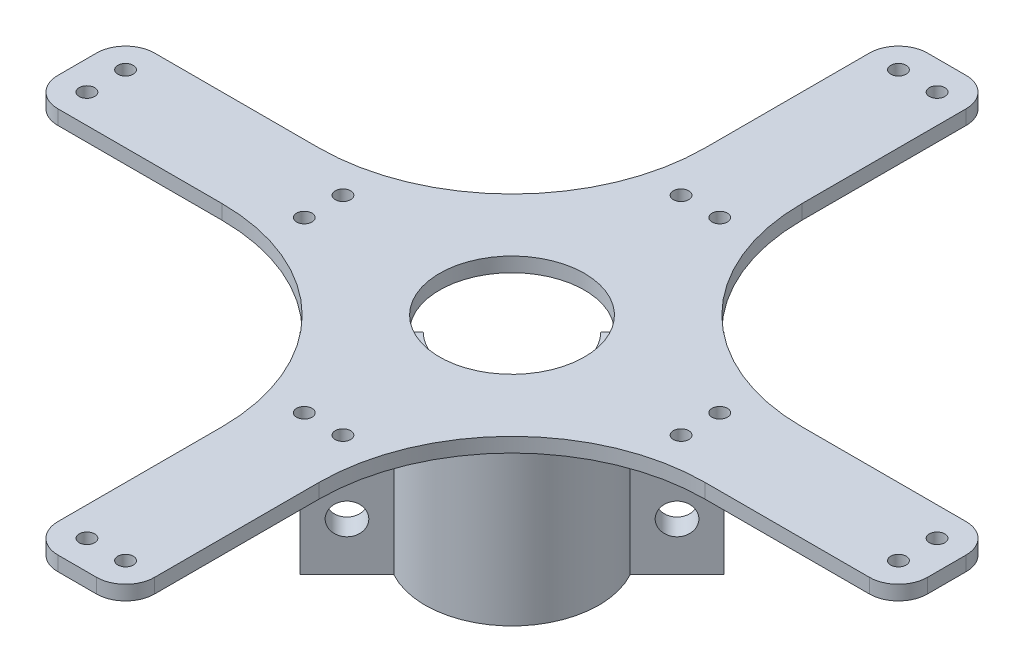
SolidWorks part; units mm, degrees
material "PLA"
ref_plane "Front Plane" through (0, 0, 0) normal (0, 0, 1) x (1, 0, 0)
ref_plane "Top Plane" through (0, 0, 0) normal (0, 1, 0) x (1, 0, 0)
ref_plane "Right Plane" through (0, 0, 0) normal (1, 0, 0) x (0, 0, -1)
sketch "Sketch1" plane through (0, 0, 0) normal (0, 1, 0) x (1, 0, 0)
  line L0 (0, 90) -> (0, -90) construction
  line L1 (-90, 0) -> (90, 0) construction
  line L2 (50, 10) -> (84, 10)
  line L3 (4, 90) -> (-4, 90)
  line L4 (10, 84) -> (10, 50)
  line L5 (4, -90) -> (-4, -90)
  line L6 (-10, 84) -> (-10, 50)
  line L7 (-84, 10) -> (-50, 10)
  line L8 (-90, 4) -> (-90, -4)
  line L9 (-84, -10) -> (-50, -10)
  line L10 (90, 4) -> (90, -4)
  line L11 (10, -50) -> (10, -84)
  line L12 (50, -10) -> (84, -10)
  line L13 (-10, -50) -> (-10, -84)
  arc A0 (4, 90) -> (10, 84) centre (4, 84) cw
  arc A1 (-4, 90) -> (-10, 84) centre (-4, 84) ccw
  arc A2 (84, 10) -> (90, 4) centre (84, 4) cw
  arc A3 (84, -10) -> (90, -4) centre (84, -4) ccw
  arc A4 (10, -84) -> (4, -90) centre (4, -84) cw
  arc A5 (-4, -90) -> (-10, -84) centre (-4, -84) cw
  arc A6 (-90, -4) -> (-84, -10) centre (-84, -4) ccw
  arc A7 (-84, 10) -> (-90, 4) centre (-84, 4) ccw
  arc A8 (50, 10) -> (10, 50) centre (50, 50) cw
  arc A9 (10, -50) -> (50, -10) centre (50, -50) cw
  arc A10 (-50, -10) -> (-10, -50) centre (-50, -50) cw
  arc A11 (-10, 50) -> (-50, 10) centre (-50, 50) cw
  point P5 (0, 0)
  point P8 (0, 0)
  point P16 (0, 90)
  point P23 (10, 90)
  point P26 (-10, 90)
  point P43 (10, -10)
  point P46 (-10, -10)
  dimension "D1" = 20
  dimension "D3" = 6
  dimension "D4" = 40
  dimension "D2" = 180
extrude "Boss-Extrude1" add sketch "Sketch1" along normal mid plane 3
hole_wizard "M3 Clearance Hole1" positions "Sketch3" profile "Sketch4" hole size "M3" standard "ANSI Metric" end condition up to next
sketch "Sketch3" plane through (0, 1.5, 0) normal (0, 1, 0) x (1, 0, 0)
  line L2 (-84, 4) -> (-39, 4) construction
  line L3 (-84, 4) -> (-84, -4) construction
  line L4 (-84, -4) -> (-39, -4) construction
  line L5 (-39, 4) -> (-39, -4) construction
  line L7 (-4, 84) -> (4, 84) construction
  line L8 (-4, 84) -> (-4, 39) construction
  line L9 (-4, 39) -> (4, 39) construction
  line L10 (4, 84) -> (4, 39) construction
  line L12 (39, 4) -> (84, 4) construction
  line L13 (39, 4) -> (39, -4) construction
  line L14 (39, -4) -> (84, -4) construction
  line L15 (84, 4) -> (84, -4) construction
  line L17 (-4, -39) -> (4, -39) construction
  line L18 (-4, -39) -> (-4, -84) construction
  line L19 (-4, -84) -> (4, -84) construction
  line L20 (4, -39) -> (4, -84) construction
  point P0 (-84, 4)
  point P3 (-84, -4)
  point P6 (-4, 84)
  point P9 (4, 84)
  point P12 (84, 4)
  point P15 (84, -4)
  point P18 (4, -84)
  point P21 (-4, -84)
  point P24 (-39, 4)
  point P26 (-39, -4)
  point P28 (39, 4)
  point P30 (39, -4)
  point P32 (4, -39)
  point P34 (-4, -39)
  point P36 (-4, 39)
  point P38 (4, 39)
  dimension "D1" = 45
sketch "Sketch4" plane through (-84, 1.5, -4) normal (1, 0, 0) x (0, 0, 1)
  line L0 (0, 0) -> (0, 3)
  line L1 (0, 3) -> (1.6, 3)
  line L2 (1.6, 3) -> (1.6, 0)
  line L5 (1.6, 0) -> (0, 0)
  line L11 (0, -6.35) -> (0, 107.95) construction
  dimension "Thru Hole Dia." = 3.2
  dimension "Thru Hole Depth" = 3
sketch "Sketch5" plane through (0, 1.5, 0) normal (0, 1, 0) x (1, 0, 0)
  circle A0 centre (0, 0) radius 15
  dimension "D1" = 30
extrude "Cut-Extrude1" cut sketch "Sketch5" against normal through all both and the other way through all
sketch "Sketch6" plane through (0, -1.5, 0) normal (0, -1, 0) x (1, 0, 0)
  line L0 (-21.7157, 21.7157) -> (21.7157, -21.7157) construction
  line L1 (-15.7626, 8.6915) -> (-25.4731, 18.402)
  line L2 (-25.4731, 18.402) -> (-18.402, 25.4731)
  line L3 (-18.402, 25.4731) -> (-8.6915, 15.7626)
  line L4 (8.6915, -15.7626) -> (18.402, -25.4731)
  line L5 (18.402, -25.4731) -> (25.4731, -18.402)
  line L6 (25.4731, -18.402) -> (15.7626, -8.6915)
  circle A0 centre (0, 0) radius 13
  arc A1 (-15.7626, 8.6915) -> (8.6915, -15.7626) centre (0, 0) ccw
  arc A2 (-50, 10) -> (-10, 50) centre (-50, 50) ccw construction
  arc A3 (50, -10) -> (10, -50) centre (50, -50) ccw construction
  circle A4 centre (0, 0) radius 18 construction
  arc A5 (15.7626, -8.6915) -> (-8.6915, 15.7626) centre (0, 0) ccw
  dimension "D1" = 26
  dimension "D3" = 5
  dimension "D4" = 5
  dimension "D2" = 5
extrude "Boss-Extrude2" add sketch "Sketch6" along normal blind 40 contours L1 L2 L3 A5 L6 L5 L4 A1 | A0
hole_wizard "M6 Clearance Hole1" positions "Sketch10" profile "Sketch8" hole size "M6" standard "ANSI Metric" end condition up to next
sketch "Sketch10" plane through (3.5355, 0, 3.5355) normal (0.7071, 0, 0.7071) x (0.7071, 0, -0.7071)
  line L0 (-24.158, -41.5) -> (-24.158, -1.5) construction
  line L1 (-31.0244, -41.5) -> (-17.2916, -41.5) construction
  line L2 (-52.3259, -1.5) -> (-28.2843, -1.5) construction
  line L4 (24.158, -41.5) -> (24.158, -1.5) construction
  line L5 (31.0244, -41.5) -> (17.2916, -41.5) construction
  line L6 (249.5584, -1.5) -> (31.0244, -1.5) construction
  line L9 (-24.158, -11.5) -> (24.158, -11.5)
  line L10 (-24.158, -11.5) -> (-24.158, -31.5)
  line L11 (-24.158, -31.5) -> (24.158, -31.5)
  line L12 (24.158, -11.5) -> (24.158, -31.5)
  line L13 (-17.2916, -1.5) -> (17.2916, -1.5) construction
  point P0 (-24.158, -11.5)
  point P2 (-24.158, -31.5)
  point P4 (24.158, -11.5)
  point P6 (24.158, -31.5)
  dimension "D1" = 20
  dimension "D2" = 10
sketch "Sketch8" plane through (-13.5468, -11.5, 20.6178) normal (0, 1, 0) x (0.7071, 0, -0.7071)
  line L0 (0, 0) -> (0, 10)
  line L1 (0, 10) -> (3.2, 10)
  line L2 (3.2, 10) -> (3.2, 0)
  line L5 (3.2, 0) -> (0, 0)
  line L11 (0, -6.35) -> (0, 107.95) construction
  dimension "Thru Hole Dia." = 6.4
  dimension "Thru Hole Depth" = 10
sketch "Sketch11" plane through (0, -41.5, 0) normal (0, -1, 0) x (1, 0, 0)
  line L0 (-21.9376, 21.9376) -> (21.9376, -21.9376)
  line L1 (18.402, -25.4731) -> (25.4731, -18.402) construction
  line L6 (8.6915, -15.7626) -> (18.402, -25.4731)
  line L7 (18.402, -25.4731) -> (25.4731, -18.402)
  line L8 (25.4731, -18.402) -> (15.7626, -8.6915)
  line L9 (-8.6915, 15.7626) -> (-18.402, 25.4731)
  line L10 (-18.402, 25.4731) -> (-25.4731, 18.402)
  line L11 (-25.4731, 18.402) -> (-15.7626, 8.6915)
  line L12 (8.6915, -15.7626) -> (18.402, -25.4731)
  line L13 (18.402, -25.4731) -> (21.9376, -21.9376)
  line L16 (-21.9376, 21.9376) -> (-25.4731, 18.402)
  line L17 (-25.4731, 18.402) -> (-15.7626, 8.6915)
  arc A2 (-15.7626, 8.6915) -> (8.6915, -15.7626) centre (0, 0) ccw
  arc A3 (15.7626, -8.6915) -> (-8.6915, 15.7626) centre (0, 0) ccw
  arc A4 (-15.7626, 8.6915) -> (8.6915, -15.7626) centre (0, 0) ccw
  dimension "D1" = 0
extrude "Cut-Extrude2" cut sketch "Sketch11" against normal up to surface (40 mm away) up to face at (4, -1.5, -40.6)
equation "\"D4@Sketch6\"=\"D3@Sketch6\""
